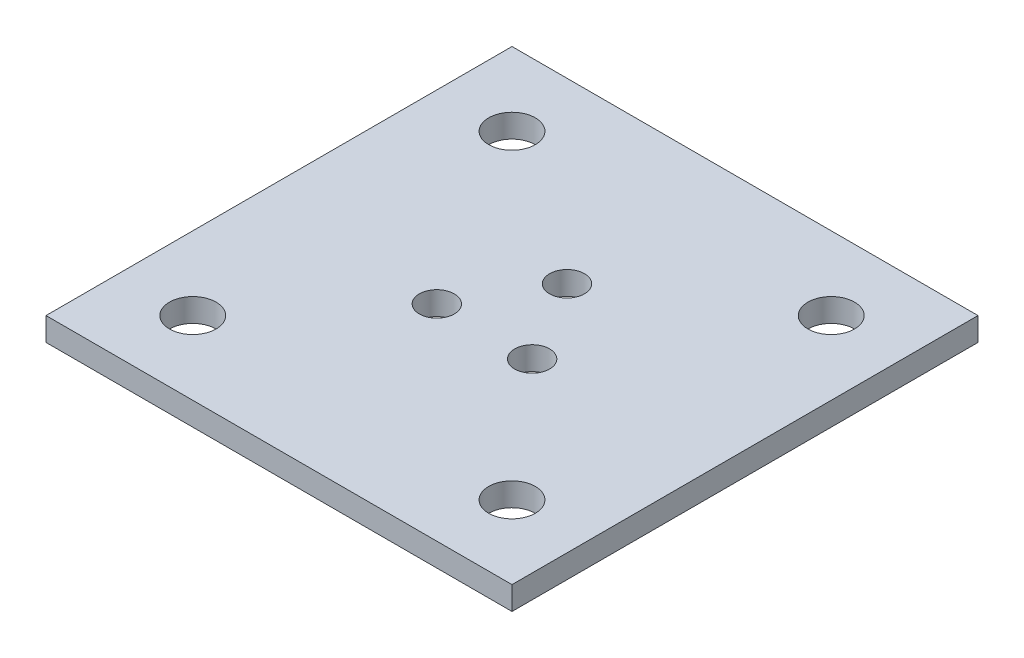
SolidWorks part; units mm, degrees
ref_plane "Front Plane" through (0, 0, 0) normal (0, 0, 1) x (1, 0, 0)
ref_plane "Top Plane" through (0, 0, 0) normal (0, 1, 0) x (1, 0, 0)
ref_plane "Right Plane" through (0, 0, 0) normal (1, 0, 0) x (0, 0, -1)
sketch "Sketch1" plane through (0, 0, 0) normal (0, 1, 0) x (1, 0, 0)
  line L1 (-31.75, -31.75) -> (31.75, -31.75)
  line L2 (-31.75, -31.75) -> (-31.75, 31.75)
  line L3 (-31.75, 31.75) -> (31.75, 31.75)
  line L4 (31.75, -31.75) -> (31.75, 31.75)
  line L5 (-31.75, -31.75) -> (31.75, 31.75) construction
  line L6 (-31.75, 31.75) -> (31.75, -31.75) construction
  circle A0 centre (0, 0) radius 19.05 construction
  dimension "D1" = 38.1
  dimension "D2" = 63.5
  dimension "D3" = 63.5
extrude "Boss-Extrude1" add sketch "Sketch1" along normal blind 3.175
sketch "Sketch2" plane through (0, 3.175, 0) normal (0, 1, 0) x (1, 0, 0)
  circle A0 centre (0, 0) radius 7.5 construction
  circle A1 centre (0, 7.5) radius 2.3812
  circle A2 centre (6.4952, -3.75) radius 2.3813
  circle A3 centre (-6.4952, -3.75) radius 2.3813
  point P11 (0, 0)
  dimension "D2" = 15
  dimension "D3" = 4.7625
  dimension "D1" = 3
extrude "Cut-Extrude1" cut sketch "Sketch2" against normal through all contours A1 | A3 | A2
sketch "Sketch3" plane through (0, 3.175, 0) normal (0, 1, 0) x (1, 0, 0)
  line L0 (-31.75, 31.75) -> (-31.75, -31.75) construction
  line L1 (-21.75, -21.75) -> (21.75, -21.75) construction
  line L2 (-21.75, -21.75) -> (-21.75, 21.75) construction
  line L3 (-21.75, 21.75) -> (21.75, 21.75) construction
  line L4 (21.75, -21.75) -> (21.75, 21.75) construction
  line L5 (-21.75, -21.75) -> (21.75, 21.75) construction
  line L6 (-21.75, 21.75) -> (21.75, -21.75) construction
  line L8 (-31.75, -31.75) -> (31.75, -31.75) construction
  circle A0 centre (-21.75, 21.75) radius 3.175
  circle A1 centre (21.75, 21.75) radius 3.175
  circle A2 centre (21.75, -21.75) radius 3.175
  circle A3 centre (-21.75, -21.75) radius 3.175
  point P0 (0, 0)
  point P17 (0, 0)
  dimension "D3" = 6.35
  dimension "D1" = 10
  dimension "D2" = 10
  dimension "D4" = 2
  dimension "D5" = 2
extrude "Cut-Extrude2" cut sketch "Sketch3" against normal through all contours A0 | A3 | A2 | A1
